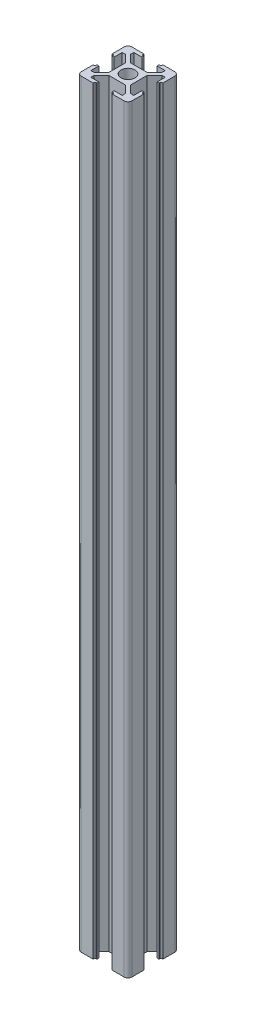
SolidWorks part; units mm, degrees
ref_plane "Front Plane" through (0, 0, 0) normal (0, 0, 1) x (1, 0, 0)
ref_plane "Top Plane" through (0, 0, 0) normal (0, 1, 0) x (1, 0, 0)
ref_plane "Right Plane" through (0, 0, 0) normal (1, 0, 0) x (0, 0, -1)
ref_plane "Plane1" through (0, 0, 0) normal (0, -1, 0) x (1, 0, 0)
sketch "Sketch1" plane through (0, 0, 0) normal (0, -1, 0) x (1, 0, 0)
  line L0 (-8.5, -10) -> (-3.75, -10)
  line L1 (-3.75, -10) -> (-3.75, -9.65)
  line L2 (-3.35, -9.25) -> (-3, -9.25)
  line L3 (-3, -9.25) -> (-3, -8.5)
  line L4 (-3, -8.5) -> (-6.2, -8.5)
  line L5 (-6.2, -8.5) -> (-6.2, -7.2607)
  line L6 (-6.2, -7.2607) -> (-3.2393, -4.3)
  line L7 (-3.2393, -4.3) -> (3.2393, -4.3)
  line L8 (3.2393, -4.3) -> (6.2, -7.2607)
  line L9 (6.2, -7.2607) -> (6.2, -8.5)
  line L10 (6.2, -8.5) -> (3, -8.5)
  line L11 (3, -8.5) -> (3, -9.25)
  line L12 (3, -9.25) -> (3.35, -9.25)
  line L13 (3.75, -9.65) -> (3.75, -10)
  line L14 (3.75, -10) -> (8.5, -10)
  line L15 (10, -8.5) -> (10, -3.75)
  line L16 (10, -3.75) -> (9.65, -3.75)
  line L17 (9.25, -3.35) -> (9.25, -3)
  line L18 (9.25, -3) -> (8.5, -3)
  line L19 (8.5, -3) -> (8.5, -6.2)
  line L20 (8.5, -6.2) -> (7.2607, -6.2)
  line L21 (7.2607, -6.2) -> (4.3, -3.2393)
  line L22 (4.3, -3.2393) -> (4.3, 3.2393)
  line L23 (4.3, 3.2393) -> (7.2607, 6.2)
  line L24 (7.2607, 6.2) -> (8.5, 6.2)
  line L25 (8.5, 6.2) -> (8.5, 3)
  line L26 (8.5, 3) -> (9.25, 3)
  line L27 (9.25, 3) -> (9.25, 3.35)
  line L28 (9.65, 3.75) -> (10, 3.75)
  line L29 (10, 3.75) -> (10, 8.5)
  line L30 (8.5, 10) -> (3.75, 10)
  line L31 (3.75, 10) -> (3.75, 9.65)
  line L32 (3.35, 9.25) -> (3, 9.25)
  line L33 (3, 9.25) -> (3, 8.5)
  line L34 (3, 8.5) -> (6.2, 8.5)
  line L35 (6.2, 8.5) -> (6.2, 7.2607)
  line L36 (6.2, 7.2607) -> (3.2393, 4.3)
  line L37 (3.2393, 4.3) -> (-3.2393, 4.3)
  line L38 (-3.2393, 4.3) -> (-6.2, 7.2607)
  line L39 (-6.2, 7.2607) -> (-6.2, 8.5)
  line L40 (-6.2, 8.5) -> (-3, 8.5)
  line L41 (-3, 8.5) -> (-3, 9.25)
  line L42 (-3, 9.25) -> (-3.35, 9.25)
  line L43 (-3.75, 9.65) -> (-3.75, 10)
  line L44 (-3.75, 10) -> (-8.5, 10)
  line L45 (-10, 8.5) -> (-10, 3.75)
  line L46 (-10, 3.75) -> (-9.65, 3.75)
  line L47 (-9.25, 3.35) -> (-9.25, 3)
  line L48 (-9.25, 3) -> (-8.5, 3)
  line L49 (-8.5, 3) -> (-8.5, 6.2)
  line L50 (-8.5, 6.2) -> (-7.2607, 6.2)
  line L51 (-7.2607, 6.2) -> (-4.3, 3.2393)
  line L52 (-4.3, 3.2393) -> (-4.3, -3.2393)
  line L53 (-4.3, -3.2393) -> (-7.2607, -6.2)
  line L54 (-7.2607, -6.2) -> (-8.5, -6.2)
  line L55 (-8.5, -6.2) -> (-8.5, -3)
  line L56 (-8.5, -3) -> (-9.25, -3)
  line L57 (-9.25, -3) -> (-9.25, -3.35)
  line L58 (-9.65, -3.75) -> (-10, -3.75)
  line L59 (-10, -3.75) -> (-10, -8.5)
  arc A0 (-10, -8.5) -> (-8.5, -10) centre (-8.5, -8.5) ccw
  arc A1 (-3.75, -9.65) -> (-3.35, -9.25) centre (-3.35, -9.65) cw
  arc A2 (3.35, -9.25) -> (3.75, -9.65) centre (3.35, -9.65) cw
  arc A3 (8.5, -10) -> (10, -8.5) centre (8.5, -8.5) ccw
  arc A4 (9.65, -3.75) -> (9.25, -3.35) centre (9.65, -3.35) cw
  arc A5 (9.25, 3.35) -> (9.65, 3.75) centre (9.65, 3.35) cw
  arc A6 (10, 8.5) -> (8.5, 10) centre (8.5, 8.5) ccw
  arc A7 (3.75, 9.65) -> (3.35, 9.25) centre (3.35, 9.65) cw
  arc A8 (-3.35, 9.25) -> (-3.75, 9.65) centre (-3.35, 9.65) cw
  arc A9 (-8.5, 10) -> (-10, 8.5) centre (-8.5, 8.5) ccw
  arc A10 (-9.65, 3.75) -> (-9.25, 3.35) centre (-9.65, 3.35) cw
  arc A11 (-9.25, -3.35) -> (-9.65, -3.75) centre (-9.65, -3.35) cw
  circle A12 centre (0, 0) radius 2.75
extrude "Boss-Extrude1" add sketch "Sketch1" against normal blind 300
